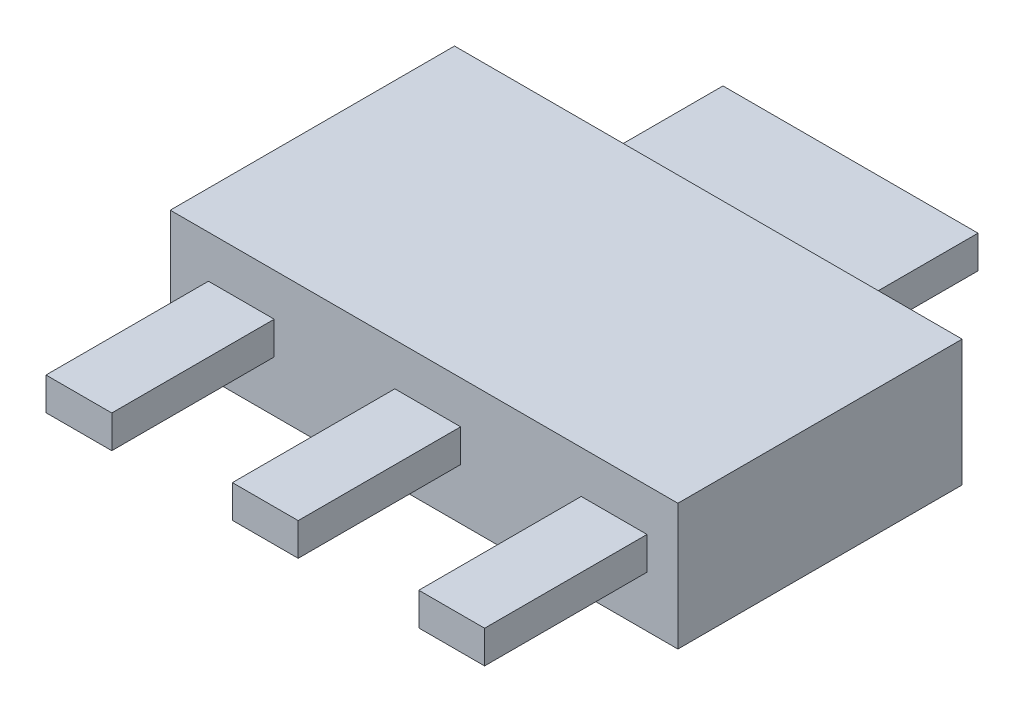
SolidWorks part; units mm, degrees
ref_plane "Front Plane" through (0, 0, 0) normal (0, 0, 1) x (1, 0, 0)
ref_plane "Top Plane" through (0, 0, 0) normal (0, 1, 0) x (1, 0, 0)
ref_plane "Right Plane" through (0, 0, 0) normal (1, 0, 0) x (0, 0, -1)
sketch "Sketch1" plane through (0, 0, 0) normal (0, 1, 0) x (1, 0, 0)
  line L1 (0, 0) -> (6.25, 0)
  line L2 (0, 0) -> (0, 3.5)
  line L3 (0, 3.5) -> (6.25, 3.5)
  line L4 (6.25, 0) -> (6.25, 3.5)
extrude "Boss-Extrude1" add sketch "Sketch1" along normal blind 1.555
sketch "Sketch2" plane through (0, 0, 0) normal (0, 0, 1) x (1, 0, 0)
  line L1 (0.47, 1.0325) -> (1.28, 1.0325)
  line L2 (0.47, 1.0325) -> (0.47, 0.63)
  line L3 (0.47, 0.63) -> (1.28, 0.63)
  line L4 (1.28, 1.0325) -> (1.28, 0.63)
  line L5 (2.765, 1.0325) -> (3.575, 1.0325)
  line L6 (2.765, 1.0325) -> (2.765, 0.63)
  line L7 (2.765, 0.63) -> (3.575, 0.63)
  line L8 (3.575, 1.0325) -> (3.575, 0.63)
  line L9 (5.06, 1.0325) -> (5.87, 1.0325)
  line L10 (5.06, 1.0325) -> (5.06, 0.63)
  line L11 (5.06, 0.63) -> (5.87, 0.63)
  line L12 (5.87, 1.0325) -> (5.87, 0.63)
  dimension "D1" = 3
sketch "Sketch5" [suppressed] plane through (6.25, 0, 0) normal (1, 0, 0) x (0, 0, -1)
  line L0 (0, 1.0325) -> (0, 0.63) construction
  spline S0 degree 3 poles (0, 0.8312) (-0.8241, 0.8771) (-1.1703, -0.02) (-2, 0) knots 0 0 0 0 1 1 1 1
extrude "Boss-Extrude8" add sketch "Sketch2" along normal blind 2 separate body
sketch "Sketch7" plane through (0, 0, -3.5) normal (0, 0, -1) x (-1, 0, 0)
  line L0 (-0.47, 0.63) -> (-1.28, 0.63) construction
  line L1 (-4.695, 1.0325) -> (-1.555, 1.0325)
  line L2 (-4.695, 1.0325) -> (-4.695, 0.63)
  line L3 (-4.695, 0.63) -> (-1.555, 0.63)
  line L4 (-1.555, 1.0325) -> (-1.555, 0.63)
  line L5 (-1.28, 1.0325) -> (-0.47, 1.0325) construction
  line L6 (-6.25, 0.7775) -> (-4.695, 0.7775) construction
  line L7 (-6.25, 1.555) -> (-6.25, 0) construction
  line L9 (-1.555, 0.7775) -> (0, 0.7775) construction
  line L10 (0, 1.555) -> (0, 0) construction
extrude "Boss-Extrude9" add sketch "Sketch7" along normal blind 1.75
